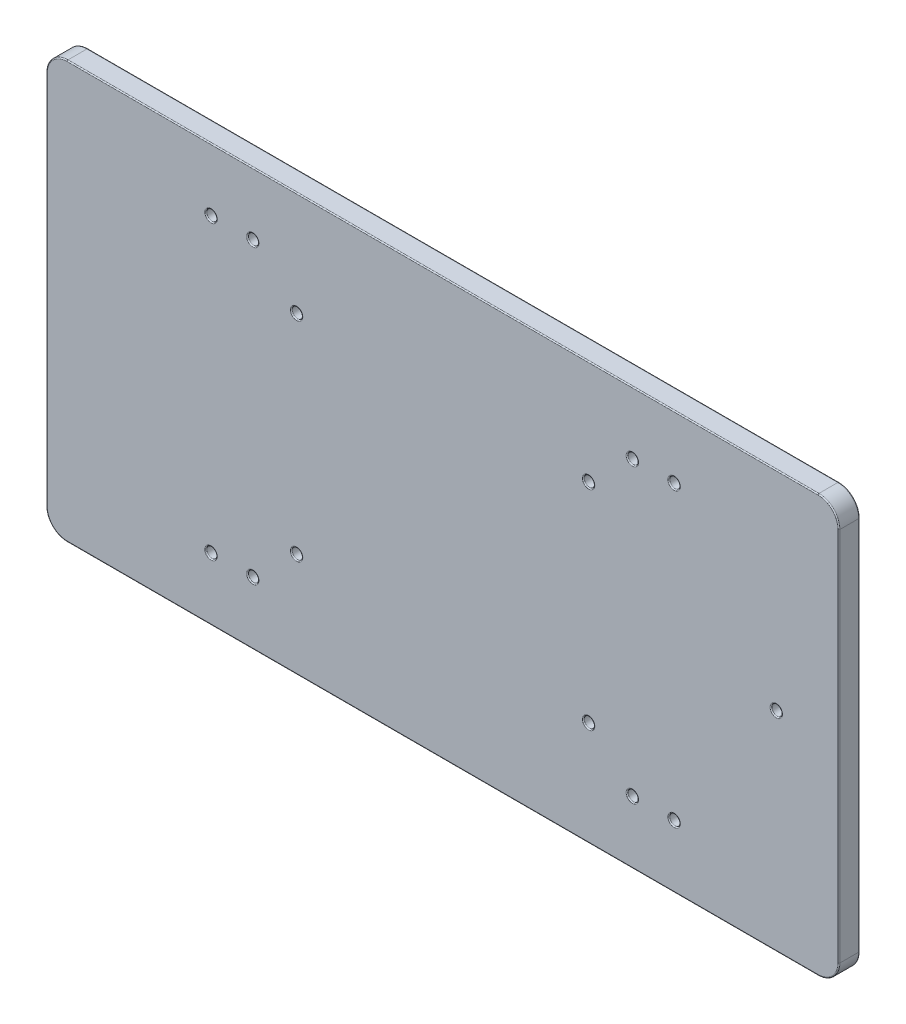
SolidWorks part; units mm, degrees
ref_plane "Front Plane" through (0, 0, 0) normal (0, 0, 1) x (1, 0, 0)
ref_plane "Top Plane" through (0, 0, 0) normal (0, 1, 0) x (1, 0, 0)
ref_plane "Right Plane" through (0, 0, 0) normal (1, 0, 0) x (0, 0, -1)
sketch "Sketch2" plane through (0, 0, 0) normal (0, 0, 1) x (1, 0, 0)
  line L0 (80, 50) -> (80, -50) construction
  line L1 (-95, 50) -> (95, 50)
  line L2 (-95, 50) -> (-95, -50)
  line L3 (-95, -50) -> (95, -50)
  line L4 (95, 50) -> (95, -50)
  line L5 (-95, 50) -> (95, -50) construction
  line L6 (-95, -50) -> (95, 50) construction
  line L7 (-35, 25) -> (35, 25) construction
  line L8 (-35, 25) -> (-35, -25) construction
  line L9 (-35, -25) -> (35, -25) construction
  line L10 (35, 25) -> (35, -25) construction
  line L11 (-35, 25) -> (35, -25) construction
  line L12 (-35, -25) -> (35, 25) construction
  line L13 (0, 0) -> (0, 19.8782) construction
  line L14 (0, 0) -> (24.4325, 0) construction
  circle A0 centre (-35, 25) radius 1.25
  circle A1 centre (35, 25) radius 1.25
  circle A2 centre (35, -25) radius 1.25
  circle A3 centre (-35, -25) radius 1.25
  circle A4 centre (80, 0) radius 1.25
  circle A5 centre (-55.5, -35) radius 1.25
  circle A6 centre (-45.5, -35) radius 1.25
  circle A7 centre (-45.5, 35) radius 1.25
  circle A8 centre (-55.5, 35) radius 1.25
  circle A9 centre (45.5, -35) radius 1.25
  circle A10 centre (55.5, -35) radius 1.25
  circle A11 centre (55.5, 35) radius 1.25
  circle A12 centre (45.5, 35) radius 1.25
  point P0 (0, 0)
  point P6 (0, 0)
  dimension "D5" = 2.5
  dimension "D7" = 2.5
  dimension "D10" = 2.5
  dimension "D1" = 190
  dimension "D2" = 100
  dimension "D3" = 70
  dimension "D4" = 50
  dimension "D6" = 15
  dimension "D8" = 10
  dimension "D9" = 15
  dimension "D11" = 45.5
extrude "Boss-Extrude1" add sketch "Sketch2" along normal blind 5
fillet "Fillet1" radius 5 4 edges at (95, -50, 2.5) (95, 50, 2.5) (-95, 50, 2.5) (-95, -50, 2.5)
fillet "Fillet2" radius 0.25 42 edges at (46.75, 35, 0) (46.75, 35, 5) (56.75, 35, 0) (56.75, 35, 5) (54.25, -35, 0) (54.25, -35, 5) (44.25, -35, 0) (44.25, -35, 5) (-56.75, 35, 0) (-56.75, 35, 5) (-46.75, 35, 0) (-46.75, 35, 5) (-44.25, -35, 0) (-44.25, -35, 5) (-54.25, -35, 0) (-54.25, -35, 5) (81.25, 0, 0) (81.25, 0, 5) (-33.75, -25, 0) (-33.75, -25, 5) (36.25, -25, 0) (36.25, -25, 5) (36.25, 25, 0) (36.25, 25, 5) (-33.75, 25, 0) (-33.75, 25, 5) (95, 0, 0) (0, 50, 0) (-95, 0, 0) (0, -50, 0) (95, 0, 5) (-95, 0, 5) (0, -50, 5) (-93.5355, -48.5355, 0) (-93.5355, 48.5355, 0) (93.5355, 48.5355, 0) (93.5355, -48.5355, 0) (-93.5355, -48.5355, 5) (-93.5355, 48.5355, 5) (93.5355, 48.5355, 5) (93.5355, -48.5355, 5) (0, 50, 5)
